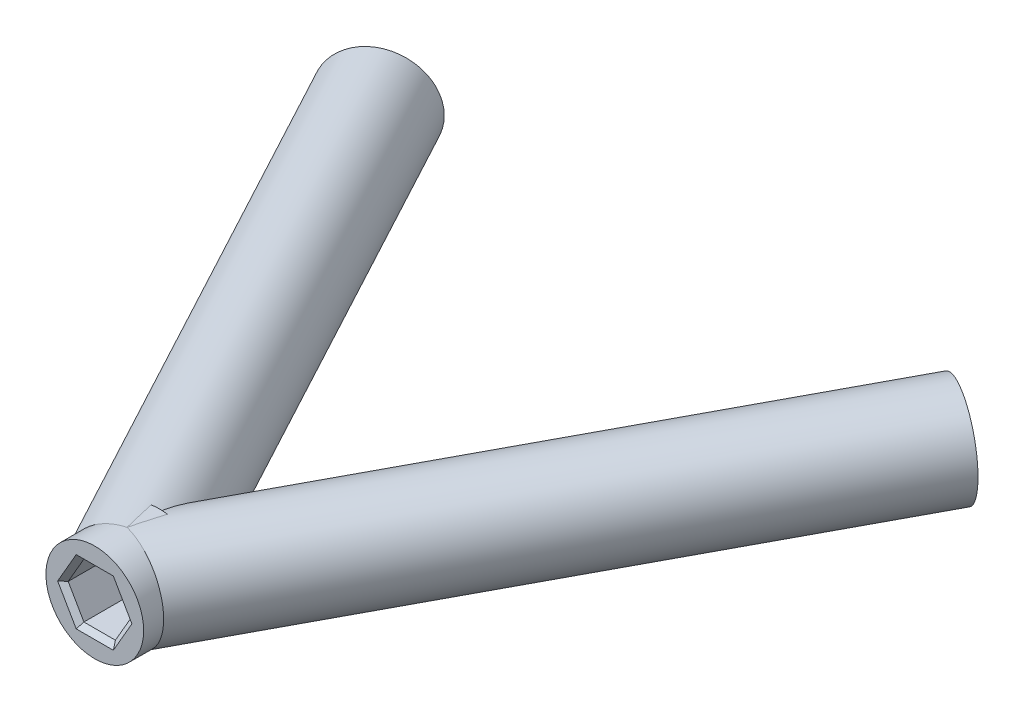
SolidWorks part; units mm, degrees
material "ABS"
ref_plane "Front Plane" through (0, 0, 0) normal (0, 0, 1) x (1, 0, 0)
ref_plane "Top Plane" through (0, 0, 0) normal (0, 1, 0) x (1, 0, 0)
ref_plane "Right Plane" through (0, 0, 0) normal (1, 0, 0) x (0, 0, -1)
sketch "Sketch1" plane through (0, 0, 0) normal (0, 1, 0) x (1, 0, 0)
  line L0 (0, 0) -> (-37.9354, 91.5842) construction
  line L1 (0, 0) -> (37.9354, 91.5842) construction
  line L2 (0, 96.1625) -> (0, 0) construction
  line L3 (0, 17.5) -> (0, 24.1)
  line L4 (-37.9354, 91.5842) -> (0, 20.8) construction
  line L5 (0, 20.8) -> (37.9354, 91.5842) construction
  line L6 (-33.2367, 0) -> (35.3523, 0) construction
  point P5 (0, 17.5)
  point P8 (0, 20.8)
  dimension "D1" = 99.13
  dimension "D2" = 45
  dimension "D3" = 17.5
  dimension "D4" = 6.6
  dimension "D5" = 56.376
  dimension "D6" = 28.188
  dimension "D7" = 28.188
revolve "Revolve-Thin2" add sketch "Sketch1" angle 360 about L3 wall 5
sketch "Sketch2" plane through (0, 0, 0) normal (0, 1, 0) x (1, 0, 0)
  line L0 (0, 96.1625) -> (0, 0) construction
  line L1 (0, 20.8) -> (37.9354, 91.5842) construction
  line L2 (-37.9354, 91.5842) -> (0, 20.8) construction
  line L3 (0, 96.1625) -> (0, 0) construction
  line L4 (0, 20.8) -> (37.9354, 91.5842) construction
  line L5 (-37.9354, 91.5842) -> (0, 20.8) construction
  point P5 (-29.6689, 76.1597)
  point P6 (29.6689, 76.1597)
  dimension "D1" = 17.5
  dimension "D2" = 17.5
  dimension "D3" = 56.376
  dimension "D4" = 80.3087
  dimension "D5" = 28.188
  dimension "D6" = 80.3087
  dimension "D7" = 80.3087
sketch3d "3DSketch1"
  line L0 (-37.9354, 0, -91.5842) -> (0, 0, -20.8) construction
sketch "Sketch3" plane through (-38.329, 0, -71.5185) normal (0.4724, 0, 0.8814) x (0.8814, 0, -0.4724)
  circle A0 centre (9.8253, 0) radius 5
  dimension "D1" = 10
extrude "Boss-Extrude1" add sketch "Sketch3" along normal up to next
sketch3d "3DSketch2"
  line L0 (0, 0, -20.8) -> (37.9354, 0, -91.5842) construction
sketch "Sketch4" plane through (38.329, 0, -71.5185) normal (-0.4724, 0, 0.8814) x (0.8814, 0, 0.4724)
  circle A0 centre (-9.8253, 0) radius 5
  dimension "D1" = 10
extrude "Boss-Extrude2" add sketch "Sketch4" along normal up to next
sketch "Sketch5" plane through (0, 0, -17.5) normal (0, 0, 1) x (1, 0, 0)
  line L1 (1.6108, 2.79) -> (-1.6108, 2.79)
  line L2 (-1.6108, 2.79) -> (-3.2216, 0)
  line L3 (-3.2216, 0) -> (-1.6108, -2.79)
  line L4 (-1.6108, -2.79) -> (1.6108, -2.79)
  line L5 (1.6108, -2.79) -> (3.2216, 0)
  line L6 (3.2216, 0) -> (1.6108, 2.79)
  circle A0 centre (0, 0) radius 2.79 construction
  dimension "D1" = 5.58
extrude "Cut-Extrude1" cut sketch "Sketch5" against normal blind 6.6
sketch "Sketch7" plane through (-38.329, 0, -71.5185) normal (-0.4724, 0, -0.8814) x (-0.8814, 0, 0.4724)
  line L1 (-7.0353, 1.6108) -> (-9.8253, 3.2216)
  line L2 (-9.8253, 3.2216) -> (-12.6153, 1.6108)
  line L3 (-12.6153, 1.6108) -> (-12.6153, -1.6108)
  line L4 (-12.6153, -1.6108) -> (-9.8253, -3.2216)
  line L5 (-9.8253, -3.2216) -> (-7.0353, -1.6108)
  line L6 (-7.0353, -1.6108) -> (-7.0353, 1.6108)
  circle A0 centre (-9.8253, 0) radius 2.79 construction
  dimension "D1" = 5.58
extrude "Cut-Extrude2" cut sketch "Sketch7" against normal blind 6.6
sketch "Sketch8" plane through (38.329, 0, -71.5185) normal (0.4724, 0, -0.8814) x (-0.8814, 0, -0.4724)
  line L1 (12.6153, 1.6108) -> (9.8253, 3.2216)
  line L2 (9.8253, 3.2216) -> (7.0353, 1.6108)
  line L3 (7.0353, 1.6108) -> (7.0353, -1.6108)
  line L4 (7.0353, -1.6108) -> (9.8253, -3.2216)
  line L5 (9.8253, -3.2216) -> (12.6153, -1.6108)
  line L6 (12.6153, -1.6108) -> (12.6153, 1.6108)
  circle A0 centre (9.8253, 0) radius 2.79 construction
  dimension "D1" = 5.58
extrude "Cut-Extrude3" cut sketch "Sketch8" against normal blind 6.6
chamfer "Chamfer1" distance 0.5 angle 45 18 edges at (-2.4162, -1.395, -17.5) (0, -2.79, -17.5) (2.4162, -1.395, -17.5) (2.4162, 1.395, -17.5) (0, 2.79, -17.5) (-2.4162, 1.395, -17.5) (28.4394, -2.4162, -76.8186) (27.2098, 0, -77.4776) (28.4394, 2.4162, -76.8186) (30.8985, 2.4162, -75.5007) (32.128, 0, -74.8418) (30.8985, -2.4162, -75.5007) (-32.128, 0, -74.8418) (-30.8985, -2.4162, -75.5007) (-28.4394, -2.4162, -76.8186) (-27.2098, 0, -77.4776) (-30.8985, 2.4162, -75.5007) (-28.4394, 2.4162, -76.8186)
